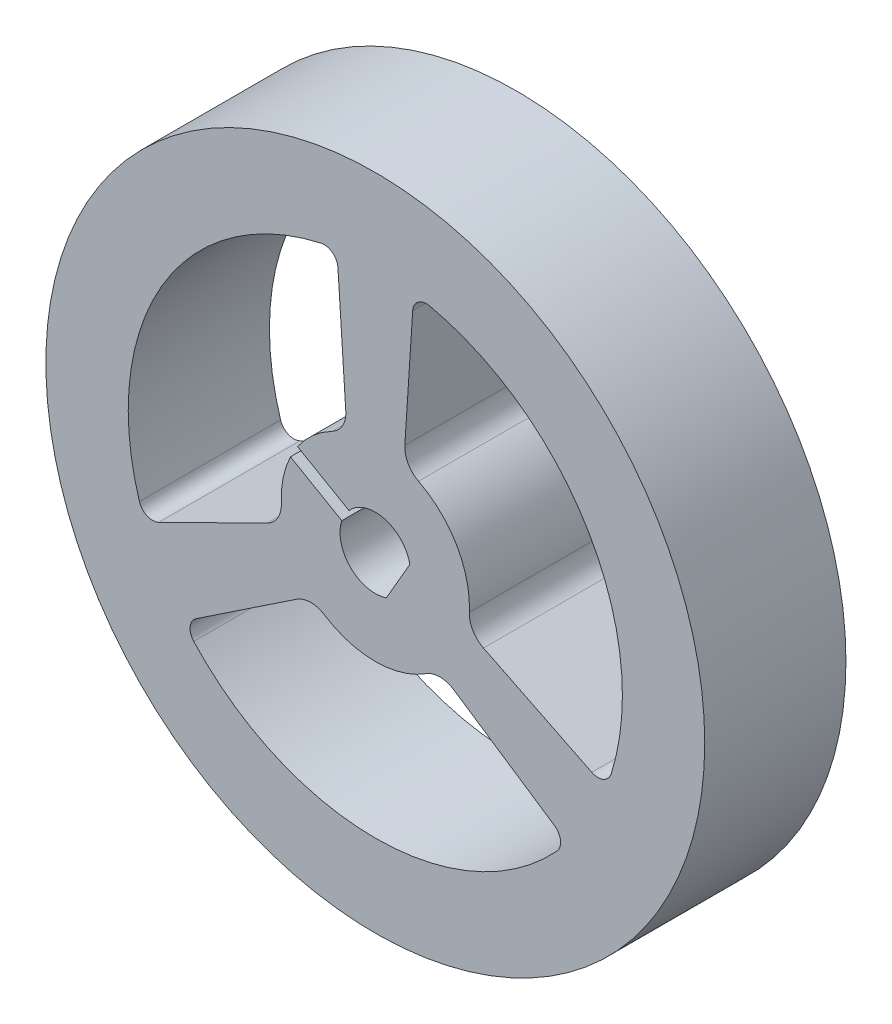
SolidWorks part; units mm, degrees
material "片状模压塑料板材"
ref_plane "前视基准面" through (0, 0, 0) normal (0, 0, 1) x (1, 0, 0)
ref_plane "上视基准面" through (0, 0, 0) normal (0, 1, 0) x (1, 0, 0)
ref_plane "右视基准面" through (0, 0, 0) normal (1, 0, 0) x (0, 0, -1)
sketch "草图1" plane through (0, 0, 0) normal (0, 0, 1) x (1, 0, 0)
  line L0 (4.597, -1.2053) -> (9.1997, -3.4771)
  line L1 (0, 0) -> (0, 3.9983) construction
  line L2 (1.2547, 4.5837) -> (1.5886, 9.7057)
  line L3 (-1.2547, 4.5837) -> (-1.5886, 9.7057)
  line L4 (3.3423, -3.3785) -> (7.6111, -6.2286)
  line L5 (-3.3423, -3.3785) -> (-7.6111, -6.2286)
  line L6 (-4.597, -1.2053) -> (-9.1997, -3.4771)
  line L7 (0, 0) -> (-2.5981, 1.5) construction
  line L8 (-1.4239, 0.4716) -> (-3.6059, 1.7313)
  line L9 (-1.1204, 0.9974) -> (-3.3023, 2.2571)
  line L10 (1.4682, 0.307) -> (0.4682, -1.425)
  circle A0 centre (0, 0) radius 14
  arc A1 (-2.3076, 10.2433) -> (-10.0247, -3.1232) centre (0, 0) ccw
  arc A2 (-1.8369, 3.5533) -> (-3.3023, 2.2571) centre (0, 0) ccw
  arc A3 (1.4682, 0.307) -> (-1.1204, 0.9974) centre (0, 0) ccw
  arc A4 (-1.8369, 3.5533) -> (-1.2547, 4.5837) centre (-2.3332, 4.5134) ccw
  arc A5 (-1.5886, 9.7057) -> (-2.3076, 10.2433) centre (-2.1778, 9.6673) ccw
  arc A6 (1.8369, 3.5533) -> (1.2547, 4.5837) centre (2.3332, 4.5134) cw
  arc A7 (1.5886, 9.7057) -> (2.3076, 10.2433) centre (2.1778, 9.6673) cw
  arc A8 (3.9957, -0.1858) -> (4.597, -1.2053) centre (5.0753, -0.2361) ccw
  arc A9 (2.1588, -3.3674) -> (3.3423, -3.3785) centre (2.7421, -4.2773) cw
  arc A10 (7.6111, -6.2286) -> (7.7172, -7.1201) centre (7.2832, -6.7197) cw
  arc A11 (9.1997, -3.4771) -> (10.0247, -3.1232) centre (9.461, -2.9476) ccw
  arc A12 (-2.1588, -3.3674) -> (-3.3423, -3.3785) centre (-2.7421, -4.2773) ccw
  arc A13 (-3.9957, -0.1858) -> (-4.597, -1.2053) centre (-5.0753, -0.2361) cw
  arc A14 (-9.1997, -3.4771) -> (-10.0247, -3.1232) centre (-9.461, -2.9476) cw
  arc A15 (-7.6111, -6.2286) -> (-7.7172, -7.1201) centre (-7.2832, -6.7197) ccw
  arc A16 (3.9957, -0.1858) -> (1.8369, 3.5533) centre (0, 0) ccw
  arc A17 (10.0247, -3.1232) -> (2.3076, 10.2433) centre (0, 0) ccw
  arc A18 (-2.1588, -3.3674) -> (2.1588, -3.3674) centre (0, 0) ccw
  arc A19 (-7.7172, -7.1201) -> (7.7172, -7.1201) centre (0, 0) ccw
  arc A20 (-1.4239, 0.4716) -> (0.4682, -1.425) centre (0, 0) ccw
  arc A21 (-3.6059, 1.7313) -> (-3.9957, -0.1858) centre (0, 0) ccw
  point P49 (0, 0)
  dimension "D1" = 28
  dimension "D2" = 21
  dimension "D3" = 8
  dimension "D4" = 3
  dimension "D5" = 1.1809
  dimension "D7" = 2
  dimension "D8" = 5.1329
  dimension "D6" = 3
extrude "凸台-拉伸1" add sketch "草图1" along normal blind 6
